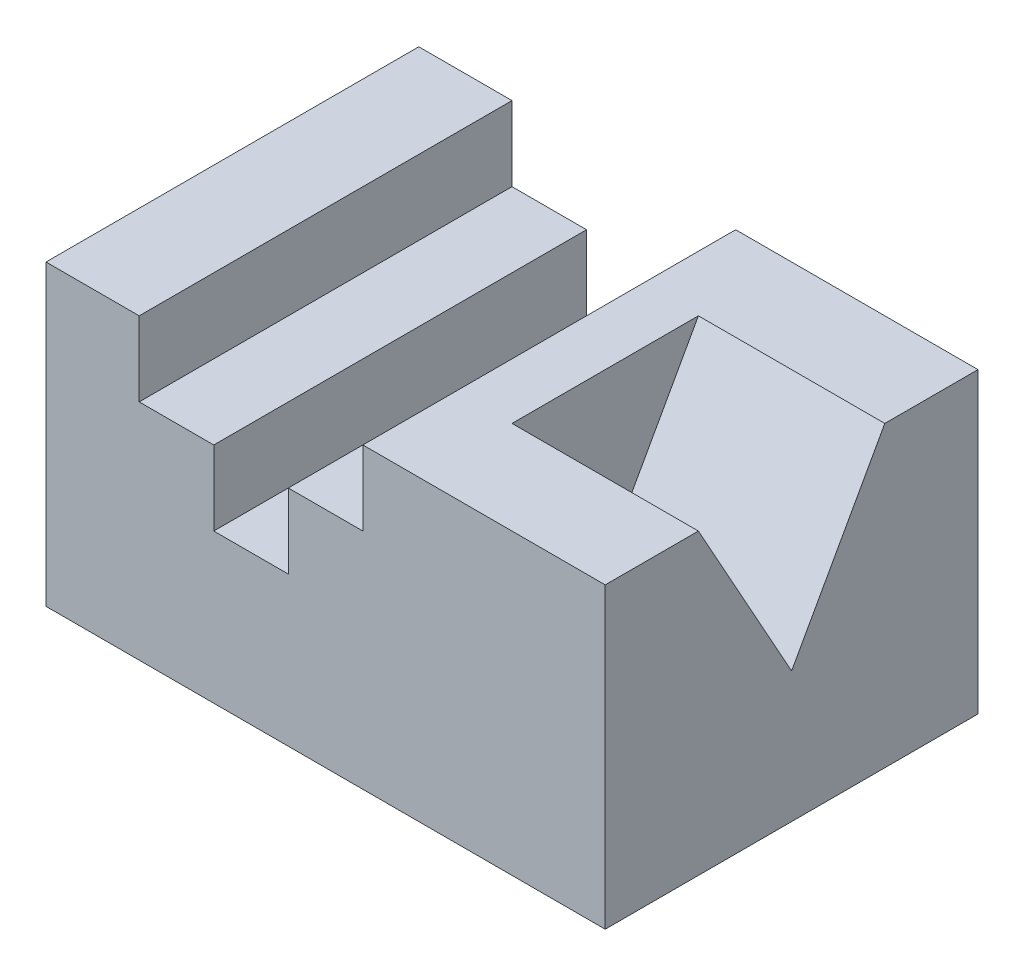
SolidWorks part; units mm, degrees
ref_plane "Front Plane" through (0, 0, 0) normal (0, 0, 1) x (1, 0, 0)
ref_plane "Top Plane" through (0, 0, 0) normal (0, 1, 0) x (1, 0, 0)
ref_plane "Right Plane" through (0, 0, 0) normal (1, 0, 0) x (0, 0, -1)
sketch "Sketch1" plane through (0, 0, 0) normal (0, 1, 0) x (1, 0, 0)
  line L0 (-75, 50) -> (75, 50)
  line L1 (75, 50) -> (75, -50)
  line L2 (75, -50) -> (-75, -50)
  line L3 (-75, -50) -> (-75, 50)
  line L4 (0, 0) -> (0, 75.3906) construction
  line L5 (0, 0) -> (161.5234, 0) construction
  dimension "D1" = 50
  dimension "D2" = 75
  dimension "D3" = 150
  dimension "D4" = 100
extrude "Boss-Extrude1" add sketch "Sketch1" along normal blind 80
sketch "Sketch2" plane through (75, 0, 0) normal (1, 0, 0) x (0, 0, -1)
  line L0 (-25, 80) -> (25, 80)
  line L1 (-50, 80) -> (50, 80) construction
  line L2 (25, 80) -> (0, 35)
  line L3 (0, 35) -> (-25, 80)
  line L4 (-50, 80) -> (-50, 0) construction
  dimension "D1" = 25
  dimension "D2" = 25
  dimension "D3" = 45
  dimension "D4" = 50
extrude "Cut-Extrude1" cut sketch "Sketch2" against normal blind 50
sketch "Sketch3" plane through (0, 0, 50) normal (0, 0, 1) x (1, 0, 0)
  line L0 (-75, 80) -> (-50, 80)
  line L1 (-75, 80) -> (75, 80) construction
  line L2 (-50, 80) -> (-50, 60)
  line L3 (-50, 60) -> (-30, 60)
  line L4 (-30, 60) -> (-30, 40)
  line L5 (-10, 40) -> (-10, 60)
  line L6 (-10, 60) -> (10, 60)
  line L7 (10, 60) -> (10, 80)
  line L8 (-30, 40) -> (-10, 40)
  dimension "D1" = 20
  dimension "D2" = 25
extrude "Cut-Extrude2" cut sketch "Sketch3" against normal through all and the other way through all
